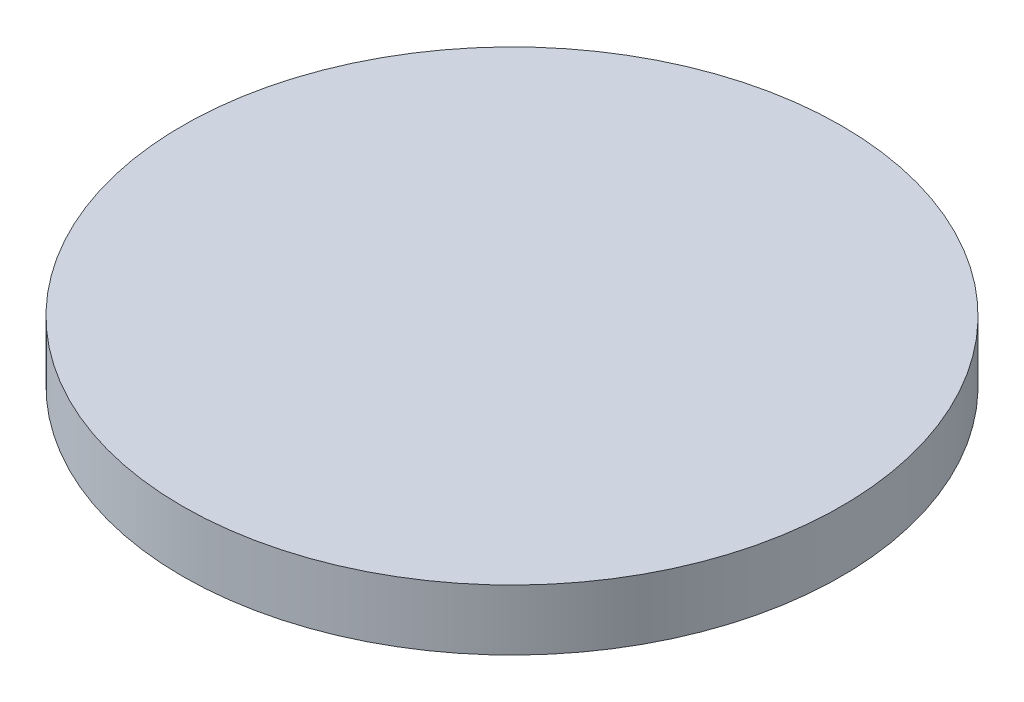
SolidWorks part; units mm, degrees
ref_plane "前视基准面" through (0, 0, 0) normal (0, 0, 1) x (1, 0, 0)
ref_plane "上视基准面" through (0, 0, 0) normal (0, 1, 0) x (1, 0, 0)
ref_plane "右视基准面" through (0, 0, 0) normal (1, 0, 0) x (0, 0, -1)
sketch "草图1" plane through (0, 0, 0) normal (0, 1, 0) x (1, 0, 0)
  circle A0 centre (0, 0) radius 12.5
  dimension "D1" = 25
extrude "凸台-拉伸1" add sketch "草图1" along normal blind 2.3
